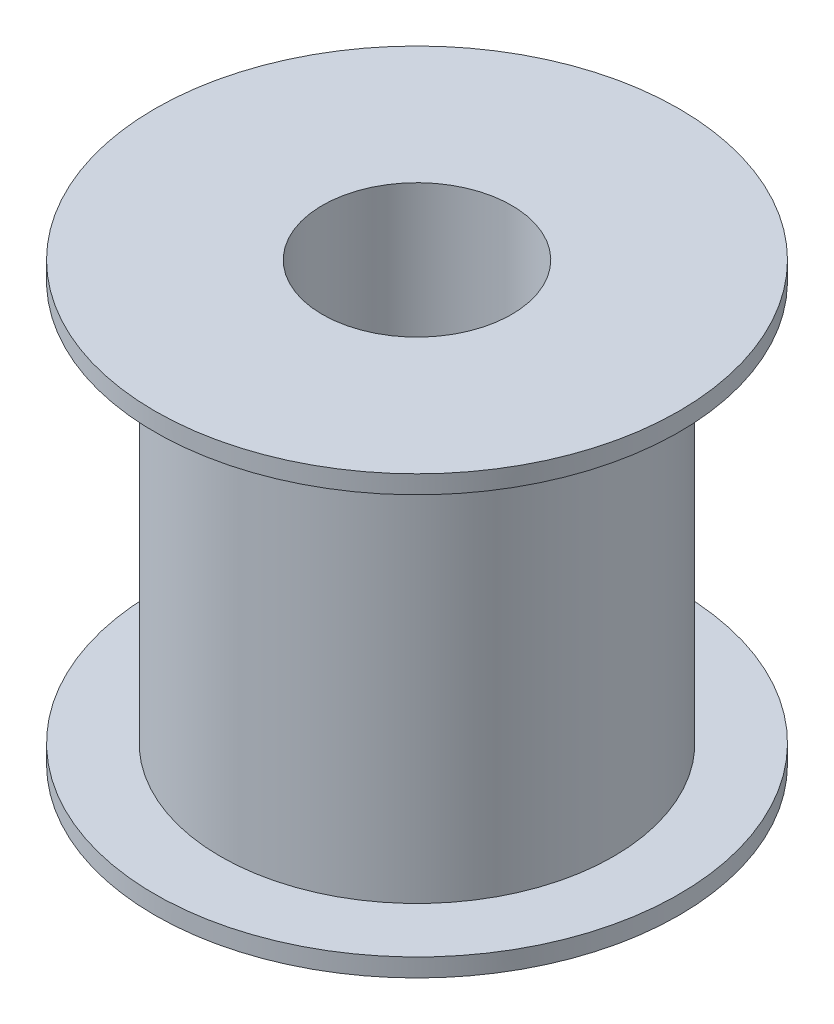
SolidWorks part; units mm, degrees
material "ABS"
ref_plane "Front Plane" through (0, 0, 0) normal (0, 0, 1) x (1, 0, 0)
ref_plane "Top Plane" through (0, 0, 0) normal (0, 1, 0) x (1, 0, 0)
ref_plane "Right Plane" through (0, 0, 0) normal (1, 0, 0) x (0, 0, -1)
sketch "Sketch1" plane through (0, 0, 0) normal (0, 1, 0) x (1, 0, 0)
  circle A0 centre (0, 0) radius 13
  circle A1 centre (0, 0) radius 36
  dimension "D1" = 26
  dimension "D2" = 72
extrude "Boss-Extrude1" add sketch "Sketch1" along normal blind 60
sketch "Sketch2" plane through (0, 0, 0) normal (0, 0, 1) x (1, 0, 0)
  line L0 (-36, 60) -> (-36, 0) construction
  line L1 (-36, 57.5) -> (-27, 57.5)
  line L2 (-36, 57.5) -> (-36, 2.5)
  line L3 (-36, 2.5) -> (-27, 2.5)
  line L4 (-27, 57.5) -> (-27, 2.5)
  line L5 (36, 60) -> (-36, 60) construction
  line L6 (-36, 0) -> (36, 0) construction
  line L7 (0, 0) -> (0, 60) construction
  line L8 (13, 60) -> (-13, 60) construction
  dimension "D1" = 2.5
  dimension "D2" = 2.5
  dimension "D3" = 9
revolve "Cut-Revolve1" cut sketch "Sketch2" angle 360 about L7
